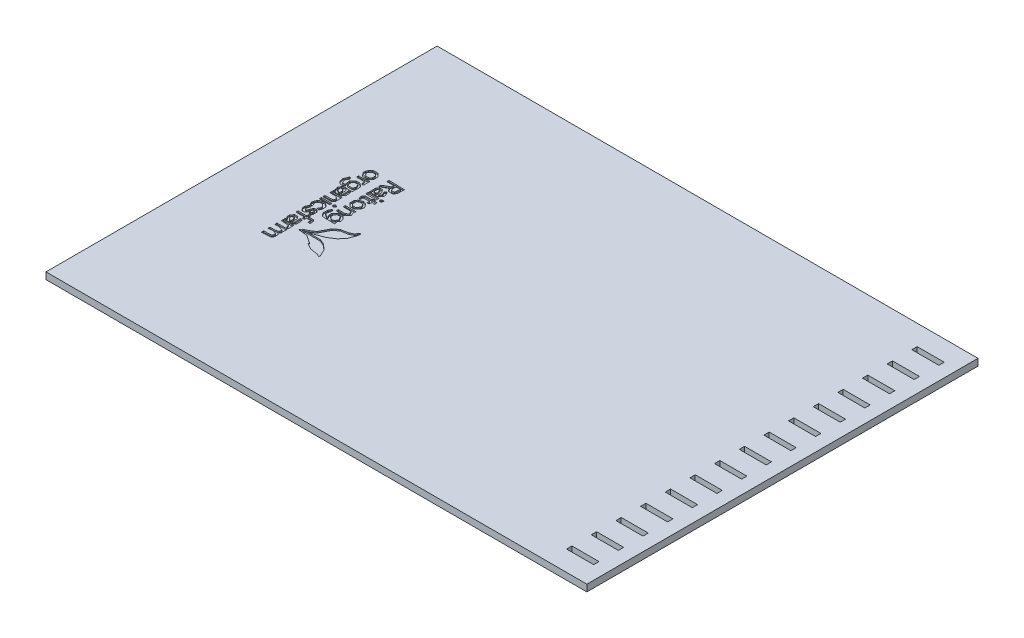
SolidWorks part; units mm, degrees
material "ABS"
ref_plane "Front Plane" through (0, 0, 0) normal (0, 0, 1) x (1, 0, 0)
ref_plane "Top Plane" through (0, 0, 0) normal (0, 1, 0) x (1, 0, 0)
ref_plane "Right Plane" through (0, 0, 0) normal (1, 0, 0) x (0, 0, -1)
sketch "Sketch1" plane through (0, 0, 0) normal (0, 1, 0) x (1, 0, 0)
  line L1 (-66.3921, 26.4776) -> (136.8079, 26.4776)
  line L2 (-66.3921, 26.4776) -> (-66.3921, -120.4614)
  line L3 (-66.3921, -120.4614) -> (136.8079, -120.4614)
  line L4 (136.8079, 26.4776) -> (136.8079, -120.4614)
  dimension "D1" = 203.2
  dimension "D2" = 146.939
extrude "Boss-Extrude1" add sketch "Sketch1" along normal blind 2.54
sketch "Sketch2" plane through (0, 2.54, 0) normal (0, 1, 0) x (0, 0, -1)
  line L14 (-120.4614, 66.3921) -> (-120.4614, -136.8079) construction
  line L15 (-110.8414, -131.7279) -> (-112.8414, -131.7279)
  line L16 (-110.8414, -131.7279) -> (-110.8414, -121.5679)
  line L17 (-110.8414, -121.5679) -> (-112.8414, -121.5679)
  line L18 (-112.8414, -131.7279) -> (-112.8414, -121.5679)
  line L19 (-120.4614, -136.8079) -> (26.4776, -136.8079) construction
  dimension "D1" = 2
  dimension "D2" = 7.62
  dimension "D3" = 5.08
  dimension "D4" = 10.16
extrude "Cut-Extrude1" cut sketch "Sketch2" against normal blind 2.794
pattern_linear "LPattern1" count 15 spacing 9.2642 along (0, 0, -1) of "Cut-Extrude1"
sketch "Sketch6" plane through (0, 2.54, 0) normal (0, 1, 0) x (1, 0, 0)
  line L8 (-40.8388, -35.001) -> (-40.6941, -35.6624)
  line L9 (-40.6941, -35.6624) -> (-40.2044, -36.1615)
  line L10 (-40.2044, -36.1615) -> (-39.7146, -36.6606)
  line L11 (-39.7146, -36.6606) -> (-38.5681, -36.6606)
  line L12 (-38.5681, -36.6606) -> (-37.4215, -36.6606)
  line L13 (-37.4215, -36.6606) -> (-37.9989, -36.8742)
  line L14 (-37.9989, -36.8742) -> (-38.5762, -37.0878)
  line L15 (-38.5762, -37.0878) -> (-38.8728, -37.6419)
  line L16 (-38.8728, -37.6419) -> (-39.1693, -38.1959)
  line L17 (-39.1693, -38.1959) -> (-38.9717, -38.7813)
  line L18 (-38.9717, -38.7813) -> (-38.774, -39.3666)
  line L19 (-38.774, -39.3666) -> (-38.8413, -39.8296)
  line L20 (-38.8413, -39.8296) -> (-38.9087, -40.2926)
  line L21 (-38.9087, -40.2926) -> (-37.4957, -40.2926)
  line L22 (-37.4957, -40.2926) -> (-36.0827, -40.2926)
  line L23 (-36.0827, -40.2926) -> (-35.4947, -39.8807)
  line L24 (-35.4947, -39.8807) -> (-34.9067, -39.4689)
  line L25 (-34.9067, -39.4689) -> (-34.9067, -38.7118)
  line L26 (-34.9067, -38.7118) -> (-34.9067, -37.9547)
  line L27 (-34.9067, -37.9547) -> (-35.0673, -37.5362)
  line L28 (-35.0673, -37.5362) -> (-35.2279, -37.1176)
  line L29 (-35.2279, -37.1176) -> (-35.5804, -37.1176)
  line L30 (-35.5804, -37.1176) -> (-35.9329, -37.1176)
  line L31 (-35.9329, -37.1176) -> (-35.8828, -38.2136)
  line L32 (-35.8828, -38.2136) -> (-35.8327, -39.3097)
  line L33 (-35.8327, -39.3097) -> (-36.1634, -39.4263)
  line L34 (-36.1634, -39.4263) -> (-36.4942, -39.543)
  line L35 (-36.4942, -39.543) -> (-36.4942, -38.6138)
  line L36 (-36.4942, -38.6138) -> (-36.4942, -37.6846)
  line L37 (-36.4942, -37.6846) -> (-36.9099, -37.2688)
  line L38 (-36.9099, -37.2688) -> (-37.3257, -36.853)
  line L39 (-37.3257, -36.853) -> (-36.1446, -36.853)
  line L40 (-36.1446, -36.853) -> (-34.9635, -36.853)
  line L41 (-34.9635, -36.853) -> (-34.9414, -35.2798)
  line L42 (-34.9414, -35.2798) -> (-34.9193, -33.7065)
  line L43 (-34.9193, -33.7065) -> (-35.6101, -33.1631)
  line L44 (-35.6101, -33.1631) -> (-36.301, -32.6197)
  line L45 (-36.301, -32.6197) -> (-37.0129, -32.6197)
  line L46 (-37.0129, -32.6197) -> (-37.7249, -32.6197)
  line L47 (-37.7249, -32.6197) -> (-38.331, -33.2649)
  line L48 (-38.331, -33.2649) -> (-38.9371, -33.9101)
  line L49 (-38.9371, -33.9101) -> (-38.8271, -34.8524)
  line L50 (-38.8271, -34.8524) -> (-38.7171, -35.7947)
  line L51 (-38.7171, -35.7947) -> (-39.1988, -35.7947)
  line L52 (-39.1988, -35.7947) -> (-39.6805, -35.7947)
  line L53 (-39.6805, -35.7947) -> (-39.977, -35.1441)
  line L54 (-39.977, -35.1441) -> (-40.2734, -34.4935)
  line L55 (-40.2734, -34.4935) -> (-39.8801, -33.8873)
  line L56 (-39.8801, -33.8873) -> (-39.4868, -33.2812)
  line L57 (-39.4868, -33.2812) -> (-39.6, -32.9504)
  line L58 (-39.6, -32.9504) -> (-39.7133, -32.6197)
  line L59 (-39.7133, -32.6197) -> (-39.9686, -32.6197)
  line L60 (-39.9686, -32.6197) -> (-40.2239, -32.6197)
  line L61 (-40.2239, -32.6197) -> (-40.6036, -33.4796)
  line L62 (-40.6036, -33.4796) -> (-40.9834, -34.3395)
  line L63 (-40.9834, -34.3395) -> (-40.8388, -35.001)
  line L64 (-38.3463, -38.4468) -> (-38.3463, -37.9426)
  line L65 (-38.3463, -37.9426) -> (-38.0415, -37.7543)
  line L66 (-38.0415, -37.7543) -> (-37.7368, -37.5659)
  line L67 (-37.7368, -37.5659) -> (-37.3801, -38.0538)
  line L68 (-37.3801, -38.0538) -> (-37.0233, -38.5417)
  line L69 (-37.0233, -38.5417) -> (-37.0233, -39.0203)
  line L70 (-37.0233, -39.0203) -> (-37.0233, -39.4989)
  line L71 (-37.0233, -39.4989) -> (-37.173, -39.4989)
  line L72 (-37.173, -39.4989) -> (-37.3227, -39.4989)
  line L73 (-37.3227, -39.4989) -> (-37.8345, -39.225)
  line L74 (-37.8345, -39.225) -> (-38.3463, -38.9511)
  line L75 (-38.3463, -38.9511) -> (-38.3463, -38.4468)
  line L76 (-38.0274, -34.8674) -> (-38.1055, -34.0723)
  line L77 (-38.1055, -34.0723) -> (-37.7761, -33.7429)
  line L78 (-37.7761, -33.7429) -> (-37.4467, -33.4135)
  line L79 (-37.4467, -33.4135) -> (-36.8324, -33.4135)
  line L80 (-36.8324, -33.4135) -> (-36.2183, -33.4135)
  line L81 (-36.2183, -33.4135) -> (-35.9075, -34.0955)
  line L82 (-35.9075, -34.0955) -> (-35.5968, -34.7775)
  line L83 (-35.5968, -34.7775) -> (-35.8759, -35.22)
  line L84 (-35.8759, -35.22) -> (-36.155, -35.6624)
  line L85 (-36.155, -35.6624) -> (-37.0522, -35.6624)
  line L86 (-37.0522, -35.6624) -> (-37.9494, -35.6624)
  line L87 (-37.9494, -35.6624) -> (-38.0274, -34.8674)
  line L88 (-39.1191, -28.1522) -> (-39.14, -28.5796)
  line L89 (-39.14, -28.5796) -> (-38.5916, -29.2767)
  line L90 (-38.5916, -29.2767) -> (-38.0433, -29.9739)
  line L91 (-38.0433, -29.9739) -> (-37.0041, -29.9739)
  line L92 (-37.0041, -29.9739) -> (-35.965, -29.9739)
  line L93 (-35.965, -29.9739) -> (-35.4358, -29.4447)
  line L94 (-35.4358, -29.4447) -> (-34.9067, -28.9155)
  line L95 (-34.9067, -28.9155) -> (-34.9067, -28.0727)
  line L96 (-34.9067, -28.0727) -> (-34.9067, -27.2298)
  line L97 (-34.9067, -27.2298) -> (-35.482, -26.6175)
  line L98 (-35.482, -26.6175) -> (-36.0572, -26.0051)
  line L99 (-36.0572, -26.0051) -> (-37.0285, -26.0051)
  line L100 (-37.0285, -26.0051) -> (-37.9997, -26.0051)
  line L101 (-37.9997, -26.0051) -> (-38.403, -26.4682)
  line L102 (-38.403, -26.4682) -> (-38.8064, -26.9312)
  line L103 (-38.8064, -26.9312) -> (-38.9523, -27.328)
  line L104 (-38.9523, -27.328) -> (-39.0982, -27.7249)
  line L105 (-39.0982, -27.7249) -> (-39.1191, -28.1522)
  line L106 (-38.3463, -27.8935) -> (-38.3463, -27.6304)
  line L107 (-38.3463, -27.6304) -> (-37.9305, -27.2147)
  line L108 (-37.9305, -27.2147) -> (-37.5147, -26.7989)
  line L109 (-37.5147, -26.7989) -> (-36.9251, -26.7989)
  line L110 (-36.9251, -26.7989) -> (-36.3354, -26.7989)
  line L111 (-36.3354, -26.7989) -> (-36.0179, -27.1164)
  line L112 (-36.0179, -27.1164) -> (-35.7004, -27.4339)
  line L113 (-35.7004, -27.4339) -> (-35.7004, -27.9895)
  line L114 (-35.7004, -27.9895) -> (-35.7004, -28.5451)
  line L115 (-35.7004, -28.5451) -> (-36.0179, -28.8626)
  line L116 (-36.0179, -28.8626) -> (-36.3354, -29.1801)
  line L117 (-36.3354, -29.1801) -> (-37.0669, -29.1801)
  line L118 (-37.0669, -29.1801) -> (-37.7985, -29.1801)
  line L119 (-37.7985, -29.1801) -> (-38.0724, -28.6684)
  line L120 (-38.0724, -28.6684) -> (-38.3463, -28.1566)
  line L121 (-38.3463, -28.1566) -> (-38.3463, -27.8935)
  line L122 (-39.1232, -47.6522) -> (-39.14, -48.0003)
  line L123 (-39.14, -48.0003) -> (-38.8661, -48.5121)
  line L124 (-38.8661, -48.5121) -> (-38.5922, -49.0239)
  line L125 (-38.5922, -49.0239) -> (-38.1764, -49.0239)
  line L126 (-38.1764, -49.0239) -> (-37.7605, -49.0239)
  line L127 (-37.7605, -49.0239) -> (-37.9511, -48.5609)
  line L128 (-37.9511, -48.5609) -> (-38.1417, -48.0978)
  line L129 (-38.1417, -48.0978) -> (-38.2645, -47.6743)
  line L130 (-38.2645, -47.6743) -> (-38.3873, -47.2507)
  line L131 (-38.3873, -47.2507) -> (-37.951, -46.8144)
  line L132 (-37.951, -46.8144) -> (-37.5147, -46.378)
  line L133 (-37.5147, -46.378) -> (-37.0233, -46.378)
  line L134 (-37.0233, -46.378) -> (-36.532, -46.378)
  line L135 (-36.532, -46.378) -> (-36.1162, -46.7938)
  line L136 (-36.1162, -46.7938) -> (-35.7004, -47.2096)
  line L137 (-35.7004, -47.2096) -> (-35.7004, -47.6669)
  line L138 (-35.7004, -47.6669) -> (-35.7004, -48.1243)
  line L139 (-35.7004, -48.1243) -> (-36.0093, -48.4331)
  line L140 (-36.0093, -48.4331) -> (-36.3181, -48.7419)
  line L141 (-36.3181, -48.7419) -> (-35.8503, -48.9215)
  line L142 (-35.8503, -48.9215) -> (-35.3824, -49.101)
  line L143 (-35.3824, -49.101) -> (-35.1486, -48.7317)
  line L144 (-35.1486, -48.7317) -> (-34.9148, -48.3624)
  line L145 (-34.9148, -48.3624) -> (-34.9107, -47.5217)
  line L146 (-34.9107, -47.5217) -> (-34.9067, -46.681)
  line L147 (-34.9067, -46.681) -> (-35.6038, -46.1327)
  line L148 (-35.6038, -46.1327) -> (-36.301, -45.5843)
  line L149 (-36.301, -45.5843) -> (-36.9441, -45.5843)
  line L150 (-36.9441, -45.5843) -> (-37.5873, -45.5843)
  line L151 (-37.5873, -45.5843) -> (-38.114, -45.8662)
  line L152 (-38.114, -45.8662) -> (-38.6407, -46.148)
  line L153 (-38.6407, -46.148) -> (-38.8736, -46.7261)
  line L154 (-38.8736, -46.7261) -> (-39.1065, -47.3041)
  line L155 (-39.1065, -47.3041) -> (-39.1232, -47.6522)
  line L156 (-39.1221, -50.8832) -> (-39.1401, -51.2874)
  line L157 (-39.1401, -51.2874) -> (-38.7282, -51.8754)
  line L158 (-38.7282, -51.8754) -> (-38.3162, -52.4635)
  line L159 (-38.3162, -52.4635) -> (-37.8171, -52.4635)
  line L160 (-37.8171, -52.4635) -> (-37.3179, -52.4635)
  line L161 (-37.3179, -52.4635) -> (-36.9061, -51.8754)
  line L162 (-36.9061, -51.8754) -> (-36.4942, -51.2874)
  line L163 (-36.4942, -51.2874) -> (-36.4942, -50.8171)
  line L164 (-36.4942, -50.8171) -> (-36.4942, -50.3468)
  line L165 (-36.4942, -50.3468) -> (-36.0973, -50.3468)
  line L166 (-36.0973, -50.3468) -> (-35.7004, -50.3468)
  line L167 (-35.7004, -50.3468) -> (-35.7004, -50.728)
  line L168 (-35.7004, -50.728) -> (-35.7004, -51.1093)
  line L169 (-35.7004, -51.1093) -> (-35.965, -51.2728)
  line L170 (-35.965, -51.2728) -> (-36.2296, -51.4364)
  line L171 (-36.2296, -51.4364) -> (-36.2296, -51.6936)
  line L172 (-36.2296, -51.6936) -> (-36.2296, -51.9509)
  line L173 (-36.2296, -51.9509) -> (-35.806, -52.1134)
  line L174 (-35.806, -52.1134) -> (-35.3824, -52.276)
  line L175 (-35.3824, -52.276) -> (-35.1486, -51.9067)
  line L176 (-35.1486, -51.9067) -> (-34.9148, -51.5374)
  line L177 (-34.9148, -51.5374) -> (-34.9107, -50.8508)
  line L178 (-34.9107, -50.8508) -> (-34.9067, -50.1642)
  line L179 (-34.9067, -50.1642) -> (-35.426, -49.6942)
  line L180 (-35.426, -49.6942) -> (-35.9453, -49.2243)
  line L181 (-35.9453, -49.2243) -> (-36.364, -49.3849)
  line L182 (-36.364, -49.3849) -> (-36.7827, -49.5456)
  line L183 (-36.7827, -49.5456) -> (-37.1788, -50.4937)
  line L184 (-37.1788, -50.4937) -> (-37.5749, -51.4418)
  line L185 (-37.5749, -51.4418) -> (-37.8944, -51.3288)
  line L186 (-37.8944, -51.3288) -> (-38.214, -51.2159)
  line L187 (-38.214, -51.2159) -> (-38.1648, -50.8475)
  line L188 (-38.1648, -50.8475) -> (-38.1156, -50.4791)
  line L189 (-38.1156, -50.4791) -> (-37.9355, -49.8838)
  line L190 (-37.9355, -49.8838) -> (-37.7554, -49.2885)
  line L191 (-37.7554, -49.2885) -> (-38.1427, -49.2885)
  line L192 (-38.1427, -49.2885) -> (-38.53, -49.2885)
  line L193 (-38.53, -49.2885) -> (-38.8171, -49.8838)
  line L194 (-38.8171, -49.8838) -> (-39.1042, -50.4791)
  line L195 (-39.1042, -50.4791) -> (-39.1221, -50.8832)
  line L196 (-39.1401, -56.7401) -> (-39.1401, -57.1947)
  line L197 (-39.1401, -57.1947) -> (-38.9003, -57.3429)
  line L198 (-38.9003, -57.3429) -> (-38.6606, -57.4911)
  line L199 (-38.6606, -57.4911) -> (-38.7989, -58.02)
  line L200 (-38.7989, -58.02) -> (-38.9372, -58.5489)
  line L201 (-38.9372, -58.5489) -> (-37.3378, -58.5489)
  line L202 (-37.3378, -58.5489) -> (-35.7383, -58.5489)
  line L203 (-35.7383, -58.5489) -> (-35.3225, -58.1331)
  line L204 (-35.3225, -58.1331) -> (-34.9067, -57.7173)
  line L205 (-34.9067, -57.7173) -> (-34.9067, -56.9641)
  line L206 (-34.9067, -56.9641) -> (-34.9067, -56.2109)
  line L207 (-34.9067, -56.2109) -> (-35.0674, -55.7924)
  line L208 (-35.0674, -55.7924) -> (-35.228, -55.3739)
  line L209 (-35.228, -55.3739) -> (-35.6013, -55.3739)
  line L210 (-35.6013, -55.3739) -> (-35.9747, -55.3739)
  line L211 (-35.9747, -55.3739) -> (-35.9037, -56.4698)
  line L212 (-35.9037, -56.4698) -> (-35.8328, -57.5658)
  line L213 (-35.8328, -57.5658) -> (-36.1635, -57.6825)
  line L214 (-36.1635, -57.6825) -> (-36.4942, -57.7992)
  line L215 (-36.4942, -57.7992) -> (-36.4942, -56.87)
  line L216 (-36.4942, -56.87) -> (-36.4942, -55.9408)
  line L217 (-36.4942, -55.9408) -> (-36.91, -55.5251)
  line L218 (-36.91, -55.5251) -> (-37.3258, -55.1093)
  line L219 (-37.3258, -55.1093) -> (-37.8211, -55.1093)
  line L220 (-37.8211, -55.1093) -> (-38.3163, -55.1093)
  line L221 (-38.3163, -55.1093) -> (-38.7282, -55.6973)
  line L222 (-38.7282, -55.6973) -> (-39.1401, -56.2854)
  line L223 (-39.1401, -56.2854) -> (-39.1401, -56.7401)
  line L224 (-38.3463, -56.8086) -> (-38.3463, -56.497)
  line L225 (-38.3463, -56.497) -> (-37.9679, -56.183)
  line L226 (-37.9679, -56.183) -> (-37.5895, -55.8689)
  line L227 (-37.5895, -55.8689) -> (-37.3065, -56.3977)
  line L228 (-37.3065, -56.3977) -> (-37.0234, -56.9266)
  line L229 (-37.0234, -56.9266) -> (-37.0234, -57.3409)
  line L230 (-37.0234, -57.3409) -> (-37.0234, -57.7551)
  line L231 (-37.0234, -57.7551) -> (-37.3674, -57.7551)
  line L232 (-37.3674, -57.7551) -> (-37.7113, -57.7551)
  line L233 (-37.7113, -57.7551) -> (-38.0288, -57.4376)
  line L234 (-38.0288, -57.4376) -> (-38.3463, -57.1201)
  line L235 (-38.3463, -57.1201) -> (-38.3463, -56.8086)
  line L236 (-38.8754, -30.8999) -> (-38.8754, -31.2968)
  line L237 (-38.8754, -31.2968) -> (-37.4253, -31.2968)
  line L238 (-37.4253, -31.2968) -> (-35.9751, -31.2968)
  line L239 (-35.9751, -31.2968) -> (-35.8091, -31.9583)
  line L240 (-35.8091, -31.9583) -> (-35.643, -32.6197)
  line L241 (-35.643, -32.6197) -> (-35.2845, -32.6197)
  line L242 (-35.2845, -32.6197) -> (-34.926, -32.6197)
  line L243 (-34.926, -32.6197) -> (-34.9505, -31.3963)
  line L244 (-34.9505, -31.3963) -> (-34.9751, -30.1728)
  line L245 (-34.9751, -30.1728) -> (-36.3299, -30.3357)
  line L246 (-36.3299, -30.3357) -> (-37.6848, -30.4984)
  line L247 (-37.6848, -30.4984) -> (-38.2801, -30.5008)
  line L248 (-38.2801, -30.5008) -> (-38.8754, -30.503)
  line L249 (-38.8754, -30.503) -> (-38.8754, -30.8999)
  line L250 (-38.8754, -40.9541) -> (-38.8754, -41.351)
  line L251 (-38.8754, -41.351) -> (-37.7354, -41.351)
  line L252 (-37.7354, -41.351) -> (-36.5953, -41.351)
  line L253 (-36.5953, -41.351) -> (-36.1191, -41.6992)
  line L254 (-36.1191, -41.6992) -> (-35.6429, -42.0474)
  line L255 (-35.6429, -42.0474) -> (-35.7404, -42.5591)
  line L256 (-35.7404, -42.5591) -> (-35.8379, -43.0708)
  line L257 (-35.8379, -43.0708) -> (-37.3566, -43.1501)
  line L258 (-37.3566, -43.1501) -> (-38.8754, -43.2295)
  line L259 (-38.8754, -43.2295) -> (-38.8754, -43.6131)
  line L260 (-38.8754, -43.6131) -> (-38.8754, -43.9968)
  line L261 (-38.8754, -43.9968) -> (-37.3068, -43.9968)
  line L262 (-37.3068, -43.9968) -> (-35.7382, -43.9968)
  line L263 (-35.7382, -43.9968) -> (-35.3275, -43.5861)
  line L264 (-35.3275, -43.5861) -> (-34.9168, -43.1754)
  line L265 (-34.9168, -43.1754) -> (-34.9463, -41.8663)
  line L266 (-34.9463, -41.8663) -> (-34.9758, -40.5572)
  line L267 (-34.9758, -40.5572) -> (-36.9256, -40.5572)
  line L268 (-36.9256, -40.5572) -> (-38.8754, -40.5572)
  line L269 (-38.8754, -40.5572) -> (-38.8754, -40.9541)
  line L270 (-38.8754, -44.9228) -> (-38.8754, -45.3197)
  line L271 (-38.8754, -45.3197) -> (-36.891, -45.3197)
  line L272 (-36.891, -45.3197) -> (-34.9067, -45.3197)
  line L273 (-34.9067, -45.3197) -> (-34.9067, -44.9228)
  line L274 (-34.9067, -44.9228) -> (-34.9067, -44.526)
  line L275 (-34.9067, -44.526) -> (-36.891, -44.526)
  line L276 (-36.891, -44.526) -> (-38.8754, -44.526)
  line L277 (-38.8754, -44.526) -> (-38.8754, -44.9228)
  line L278 (-38.8754, -53.6541) -> (-38.8754, -54.051)
  line L279 (-38.8754, -54.051) -> (-37.2879, -54.051)
  line L280 (-37.2879, -54.051) -> (-35.7004, -54.051)
  line L281 (-35.7004, -54.051) -> (-35.7004, -54.4478)
  line L282 (-35.7004, -54.4478) -> (-35.7004, -54.8447)
  line L283 (-35.7004, -54.8447) -> (-35.3035, -54.8447)
  line L284 (-35.3035, -54.8447) -> (-34.9067, -54.8447)
  line L285 (-34.9067, -54.8447) -> (-34.9067, -54.4478)
  line L286 (-34.9067, -54.4478) -> (-34.9067, -54.051)
  line L287 (-34.9067, -54.051) -> (-34.1129, -54.051)
  line L288 (-34.1129, -54.051) -> (-33.3192, -54.051)
  line L289 (-33.3192, -54.051) -> (-33.3192, -54.5801)
  line L290 (-33.3192, -54.5801) -> (-33.3192, -55.1093)
  line L291 (-33.3192, -55.1093) -> (-32.9223, -55.1093)
  line L292 (-32.9223, -55.1093) -> (-32.5254, -55.1093)
  line L293 (-32.5254, -55.1093) -> (-32.5254, -54.5008)
  line L294 (-32.5254, -54.5008) -> (-32.5254, -53.8922)
  line L295 (-32.5254, -53.8922) -> (-32.8429, -53.5747)
  line L296 (-32.8429, -53.5747) -> (-33.1604, -53.2572)
  line L297 (-33.1604, -53.2572) -> (-34.0335, -53.2572)
  line L298 (-34.0335, -53.2572) -> (-34.9067, -53.2572)
  line L299 (-34.9067, -53.2572) -> (-34.9067, -52.8603)
  line L300 (-34.9067, -52.8603) -> (-34.9067, -52.4635)
  line L301 (-34.9067, -52.4635) -> (-35.3035, -52.4635)
  line L302 (-35.3035, -52.4635) -> (-35.7004, -52.4635)
  line L303 (-35.7004, -52.4635) -> (-35.7004, -52.8603)
  line L304 (-35.7004, -52.8603) -> (-35.7004, -53.2572)
  line L305 (-35.7004, -53.2572) -> (-37.2879, -53.2572)
  line L306 (-37.2879, -53.2572) -> (-38.8754, -53.2572)
  line L307 (-38.8754, -53.2572) -> (-38.8754, -53.6541)
  line L308 (-38.8754, -59.1965) -> (-38.8754, -59.5796)
  line L309 (-38.8754, -59.5796) -> (-37.4863, -59.6595)
  line L310 (-37.4863, -59.6595) -> (-36.0973, -59.7395)
  line L311 (-36.0973, -59.7395) -> (-35.8361, -60.3348)
  line L312 (-35.8361, -60.3348) -> (-35.5749, -60.9301)
  line L313 (-35.5749, -60.9301) -> (-35.2574, -60.9301)
  line L314 (-35.2574, -60.9301) -> (-34.9398, -60.9301)
  line L315 (-34.9398, -60.9301) -> (-34.9544, -59.8718)
  line L316 (-34.9544, -59.8718) -> (-34.9691, -58.8135)
  line L317 (-34.9691, -58.8135) -> (-36.9222, -58.8135)
  line L318 (-36.9222, -58.8135) -> (-38.8754, -58.8135)
  line L319 (-38.8754, -58.8135) -> (-38.8754, -59.1965)
  line L320 (-38.8754, -61.5916) -> (-38.8754, -61.9885)
  line L321 (-38.8754, -61.9885) -> (-37.9666, -61.9885)
  line L322 (-37.9666, -61.9885) -> (-37.0578, -61.9885)
  line L323 (-37.0578, -61.9885) -> (-36.3791, -62.2465)
  line L324 (-36.3791, -62.2465) -> (-35.7004, -62.5045)
  line L325 (-35.7004, -62.5045) -> (-35.7004, -63.0094)
  line L326 (-35.7004, -63.0094) -> (-35.7004, -63.5143)
  line L327 (-35.7004, -63.5143) -> (-36.2957, -63.6738)
  line L328 (-36.2957, -63.6738) -> (-36.891, -63.8333)
  line L329 (-36.891, -63.8333) -> (-37.8832, -63.8369)
  line L330 (-37.8832, -63.8369) -> (-38.8754, -63.8406)
  line L331 (-38.8754, -63.8406) -> (-38.8754, -64.2208)
  line L332 (-38.8754, -64.2208) -> (-38.8754, -64.601)
  line L333 (-38.8754, -64.601) -> (-38.0155, -64.464)
  line L334 (-38.0155, -64.464) -> (-37.1556, -64.327)
  line L335 (-37.1556, -64.327) -> (-36.4097, -64.6134)
  line L336 (-36.4097, -64.6134) -> (-35.6637, -64.8997)
  line L337 (-35.6637, -64.8997) -> (-35.7482, -65.4946)
  line L338 (-35.7482, -65.4946) -> (-35.8327, -66.0895)
  line L339 (-35.8327, -66.0895) -> (-37.3541, -66.1689)
  line L340 (-37.3541, -66.1689) -> (-38.8754, -66.2482)
  line L341 (-38.8754, -66.2482) -> (-38.8754, -66.6627)
  line L342 (-38.8754, -66.6627) -> (-38.8754, -67.0772)
  line L343 (-38.8754, -67.0772) -> (-38.3374, -67.043)
  line L344 (-38.3374, -67.043) -> (-35.3996, -66.8559)
  line L345 (-35.3996, -66.8559) -> (-35.1572, -66.4727)
  line L346 (-35.1572, -66.4727) -> (-34.9148, -66.0895)
  line L347 (-34.9148, -66.0895) -> (-34.9107, -65.3775)
  line L348 (-34.9107, -65.3775) -> (-34.9067, -64.6655)
  line L349 (-34.9067, -64.6655) -> (-35.1841, -64.4941)
  line L350 (-35.1841, -64.4941) -> (-35.4615, -64.3226)
  line L351 (-35.4615, -64.3226) -> (-35.1928, -63.9988)
  line L352 (-35.1928, -63.9988) -> (-34.924, -63.6749)
  line L353 (-34.924, -63.6749) -> (-34.9489, -62.4348)
  line L354 (-34.9489, -62.4348) -> (-34.9738, -61.1947)
  line L355 (-34.9738, -61.1947) -> (-36.9246, -61.1947)
  line L356 (-36.9246, -61.1947) -> (-38.8754, -61.1947)
  line L357 (-38.8754, -61.1947) -> (-38.8754, -61.5916)
  line L358 (-34.1129, -44.9384) -> (-34.1129, -45.3197)
  line L359 (-34.1129, -45.3197) -> (-33.7317, -45.3197)
  line L360 (-33.7317, -45.3197) -> (-33.3504, -45.3197)
  line L361 (-33.3504, -45.3197) -> (-33.1686, -45.0255)
  line L362 (-33.1686, -45.0255) -> (-32.9868, -44.7314)
  line L363 (-32.9868, -44.7314) -> (-33.3388, -44.5138)
  line L364 (-33.3388, -44.5138) -> (-33.6908, -44.2963)
  line L365 (-33.6908, -44.2963) -> (-33.9018, -44.4267)
  line L366 (-33.9018, -44.4267) -> (-34.1129, -44.5572)
  line L367 (-34.1129, -44.5572) -> (-34.1129, -44.9384)
  line L368 (-33.5659, -48.3992) -> (-33.5838, -49.2298)
  line L369 (-33.5838, -49.2298) -> (-33.0782, -49.8545)
  line L370 (-33.0782, -49.8545) -> (-32.5725, -50.4791)
  line L371 (-32.5725, -50.4791) -> (-30.1296, -50.573)
  line L372 (-30.1296, -50.573) -> (-27.6867, -50.6669)
  line L373 (-27.6867, -50.6669) -> (-27.846, -50.0576)
  line L374 (-27.846, -50.0576) -> (-28.0054, -49.4483)
  line L375 (-28.0054, -49.4483) -> (-27.7223, -49.1072)
  line L376 (-27.7223, -49.1072) -> (-27.4392, -48.7662)
  line L377 (-27.4392, -48.7662) -> (-27.6043, -48.1086)
  line L378 (-27.6043, -48.1086) -> (-27.7693, -47.451)
  line L379 (-27.7693, -47.451) -> (-28.3452, -46.9145)
  line L380 (-28.3452, -46.9145) -> (-28.921, -46.378)
  line L381 (-28.921, -46.378) -> (-29.6769, -46.378)
  line L382 (-29.6769, -46.378) -> (-30.4328, -46.378)
  line L383 (-30.4328, -46.378) -> (-31.0822, -47.0275)
  line L384 (-31.0822, -47.0275) -> (-31.7317, -47.6769)
  line L385 (-31.7317, -47.6769) -> (-31.7317, -48.2355)
  line L386 (-31.7317, -48.2355) -> (-31.7317, -48.7941)
  line L387 (-31.7317, -48.7941) -> (-31.4578, -49.3059)
  line L388 (-31.4578, -49.3059) -> (-31.1839, -49.8176)
  line L389 (-31.1839, -49.8176) -> (-31.3989, -49.8176)
  line L390 (-31.3989, -49.8176) -> (-31.6139, -49.8176)
  line L391 (-31.6139, -49.8176) -> (-32.2272, -49.3881)
  line L392 (-32.2272, -49.3881) -> (-32.8405, -48.9585)
  line L393 (-32.8405, -48.9585) -> (-32.7016, -48.2636)
  line L394 (-32.7016, -48.2636) -> (-32.5628, -47.5687)
  line L395 (-32.5628, -47.5687) -> (-32.478, -47.068)
  line L396 (-32.478, -47.068) -> (-32.3931, -46.5673)
  line L397 (-32.3931, -46.5673) -> (-32.6801, -46.4652)
  line L398 (-32.6801, -46.4652) -> (-32.9671, -46.3631)
  line L399 (-32.9671, -46.3631) -> (-33.2575, -46.9659)
  line L400 (-33.2575, -46.9659) -> (-33.5479, -47.5687)
  line L401 (-33.5479, -47.5687) -> (-33.5659, -48.3992)
  line L402 (-30.9299, -48.5198) -> (-30.9218, -48.0978)
  line L403 (-30.9218, -48.0978) -> (-30.6521, -47.6348)
  line L404 (-30.6521, -47.6348) -> (-30.3825, -47.1718)
  line L405 (-30.3825, -47.1718) -> (-29.7403, -47.1718)
  line L406 (-29.7403, -47.1718) -> (-29.098, -47.1718)
  line L407 (-29.098, -47.1718) -> (-28.6763, -47.8155)
  line L408 (-28.6763, -47.8155) -> (-28.2545, -48.4592)
  line L409 (-28.2545, -48.4592) -> (-28.5376, -48.9882)
  line L410 (-28.5376, -48.9882) -> (-28.8207, -49.5172)
  line L411 (-28.8207, -49.5172) -> (-29.3691, -49.6913)
  line L412 (-29.3691, -49.6913) -> (-29.9175, -49.8653)
  line L413 (-29.9175, -49.8653) -> (-30.4277, -49.4036)
  line L414 (-30.4277, -49.4036) -> (-30.9379, -48.9419)
  line L415 (-30.9379, -48.9419) -> (-30.9299, -48.5198)
  line L416 (-31.0663, -59.3896) -> (-29.2954, -59.5688)
  line L417 (-29.2954, -59.5688) -> (-27.8677, -60.5168)
  line L418 (-27.8677, -60.5168) -> (-26.44, -61.4647)
  line L419 (-26.44, -61.4647) -> (-26.44, -61.7154)
  line L420 (-26.44, -61.7154) -> (-26.44, -61.9662)
  line L421 (-26.44, -61.9662) -> (-25.3155, -62.6236)
  line L422 (-25.3155, -62.6236) -> (-24.191, -63.281)
  line L423 (-24.191, -63.281) -> (-22.5109, -63.5503)
  line L424 (-22.5109, -63.5503) -> (-20.8309, -63.8197)
  line L425 (-20.8309, -63.8197) -> (-20.4604, -64.1271)
  line L426 (-20.4604, -64.1271) -> (-20.09, -64.4345)
  line L427 (-20.09, -64.4345) -> (-20.0926, -64.0714)
  line L428 (-20.0926, -64.0714) -> (-20.0952, -63.7083)
  line L429 (-20.0952, -63.7083) -> (-20.7172, -62.3853)
  line L430 (-20.7172, -62.3853) -> (-21.3393, -61.0624)
  line L431 (-21.3393, -61.0624) -> (-22.3165, -60.183)
  line L432 (-22.3165, -60.183) -> (-23.2938, -59.3036)
  line L433 (-23.2938, -59.3036) -> (-24.2716, -58.8762)
  line L434 (-24.2716, -58.8762) -> (-25.2494, -58.4487)
  line L435 (-25.2494, -58.4487) -> (-27.9705, -58.4327)
  line L436 (-27.9705, -58.4327) -> (-30.6916, -58.4166)
  line L437 (-30.6916, -58.4166) -> (-29.703, -58.2111)
  line L438 (-29.703, -58.2111) -> (-28.7143, -58.0057)
  line L439 (-28.7143, -58.0057) -> (-26.8496, -57.3346)
  line L440 (-26.8496, -57.3346) -> (-24.9848, -56.6634)
  line L441 (-24.9848, -56.6634) -> (-23.7214, -55.8545)
  line L442 (-23.7214, -55.8545) -> (-22.458, -55.0456)
  line L443 (-22.458, -55.0456) -> (-21.5701, -54.0083)
  line L444 (-21.5701, -54.0083) -> (-20.6822, -52.971)
  line L445 (-20.6822, -52.971) -> (-20.1215, -51.4333)
  line L446 (-20.1215, -51.4333) -> (-19.5608, -49.8956)
  line L447 (-19.5608, -49.8956) -> (-19.5608, -49.4597)
  line L448 (-19.5608, -49.4597) -> (-19.5608, -49.0239)
  line L449 (-19.5608, -49.0239) -> (-19.8161, -49.0239)
  line L450 (-19.8161, -49.0239) -> (-20.0714, -49.0239)
  line L451 (-20.0714, -49.0239) -> (-20.3531, -49.5503)
  line L452 (-20.3531, -49.5503) -> (-20.6349, -50.0767)
  line L453 (-20.6349, -50.0767) -> (-21.4209, -50.4832)
  line L454 (-21.4209, -50.4832) -> (-22.207, -50.8897)
  line L455 (-22.207, -50.8897) -> (-23.5726, -51.1487)
  line L456 (-23.5726, -51.1487) -> (-24.9382, -51.4077)
  line L457 (-24.9382, -51.4077) -> (-25.8091, -52.072)
  line L458 (-25.8091, -52.072) -> (-26.68, -52.7362)
  line L459 (-26.68, -52.7362) -> (-27.6648, -54.6102)
  line L460 (-27.6648, -54.6102) -> (-28.6495, -56.4842)
  line L461 (-28.6495, -56.4842) -> (-29.6743, -57.1311)
  line L462 (-29.6743, -57.1311) -> (-30.6991, -57.778)
  line L463 (-30.6991, -57.778) -> (-31.4138, -58.0683)
  line L464 (-31.4138, -58.0683) -> (-32.1285, -58.3585)
  line L465 (-32.1285, -58.3585) -> (-31.4671, -58.5596)
  line L466 (-31.4671, -58.5596) -> (-30.8056, -58.7607)
  line L467 (-30.8056, -58.7607) -> (-31.6214, -58.7871)
  line L468 (-31.6214, -58.7871) -> (-32.4372, -58.8135)
  line L469 (-32.4372, -58.8135) -> (-32.6372, -59.0119)
  line L470 (-32.6372, -59.0119) -> (-32.8371, -59.2104)
  line L471 (-32.8371, -59.2104) -> (-31.0663, -59.3896)
  line L472 (-31.7317, -26.6579) -> (-31.7317, -27.0635)
  line L473 (-31.7317, -27.0635) -> (-30.3894, -27.0635)
  line L474 (-30.3894, -27.0635) -> (-29.047, -27.0635)
  line L475 (-29.047, -27.0635) -> (-29.1355, -27.5229)
  line L476 (-29.1355, -27.5229) -> (-29.224, -27.9824)
  line L477 (-29.224, -27.9824) -> (-30.3657, -28.6122)
  line L478 (-30.3657, -28.6122) -> (-31.5075, -29.242)
  line L479 (-31.5075, -29.242) -> (-31.6522, -29.6194)
  line L480 (-31.6522, -29.6194) -> (-31.7971, -29.9967)
  line L481 (-31.7971, -29.9967) -> (-31.6723, -30.1214)
  line L482 (-31.6723, -30.1214) -> (-31.5475, -30.2462)
  line L483 (-31.5475, -30.2462) -> (-30.2985, -29.5481)
  line L484 (-30.2985, -29.5481) -> (-29.0494, -28.8499)
  line L485 (-29.0494, -28.8499) -> (-28.6557, -29.4119)
  line L486 (-28.6557, -29.4119) -> (-28.2621, -29.9739)
  line L487 (-28.2621, -29.9739) -> (-27.3604, -29.9739)
  line L488 (-27.3604, -29.9739) -> (-26.4586, -29.9739)
  line L489 (-26.4586, -29.9739) -> (-26.1588, -29.4136)
  line L490 (-26.1588, -29.4136) -> (-25.8589, -28.8533)
  line L491 (-25.8589, -28.8533) -> (-25.8187, -27.6276)
  line L492 (-25.8187, -27.6276) -> (-25.7785, -26.402)
  line L493 (-25.7785, -26.402) -> (-28.7551, -26.3272)
  line L494 (-28.7551, -26.3272) -> (-31.7317, -26.2524)
  line L495 (-31.7317, -26.2524) -> (-31.7317, -26.6579)
  line L496 (-28.288, -27.7911) -> (-28.2921, -27.0635)
  line L497 (-28.2921, -27.0635) -> (-27.4824, -27.0635)
  line L498 (-27.4824, -27.0635) -> (-26.6727, -27.0635)
  line L499 (-26.6727, -27.0635) -> (-26.7548, -28.0534)
  line L500 (-26.7548, -28.0534) -> (-26.8369, -29.0434)
  line L501 (-26.8369, -29.0434) -> (-27.3343, -29.1378)
  line L502 (-27.3343, -29.1378) -> (-27.8318, -29.2322)
  line L503 (-27.8318, -29.2322) -> (-28.0579, -28.8754)
  line L504 (-28.0579, -28.8754) -> (-28.284, -28.5187)
  line L505 (-28.284, -28.5187) -> (-28.288, -27.7911)
  line L506 (-31.6913, -32.4022) -> (-31.6625, -33.678)
  line L507 (-31.6625, -33.678) -> (-30.1096, -33.678)
  line L508 (-30.1096, -33.678) -> (-28.5567, -33.678)
  line L509 (-28.5567, -33.678) -> (-28.0275, -33.1489)
  line L510 (-28.0275, -33.1489) -> (-27.4983, -32.6197)
  line L511 (-27.4983, -32.6197) -> (-27.4983, -32.2353)
  line L512 (-27.4983, -32.2353) -> (-27.4983, -31.8509)
  line L513 (-27.4983, -31.8509) -> (-27.8054, -31.177)
  line L514 (-27.8054, -31.177) -> (-28.1125, -30.503)
  line L515 (-28.1125, -30.503) -> (-28.319, -30.503)
  line L516 (-28.319, -30.503) -> (-28.5254, -30.503)
  line L517 (-28.5254, -30.503) -> (-28.6856, -30.7621)
  line L518 (-28.6856, -30.7621) -> (-28.8457, -31.0213)
  line L519 (-28.8457, -31.0213) -> (-28.5699, -31.5367)
  line L520 (-28.5699, -31.5367) -> (-28.294, -32.0522)
  line L521 (-28.294, -32.0522) -> (-28.4536, -32.4682)
  line L522 (-28.4536, -32.4682) -> (-28.6133, -32.8843)
  line L523 (-28.6133, -32.8843) -> (-28.8496, -32.8843)
  line L524 (-28.8496, -32.8843) -> (-29.0858, -32.8843)
  line L525 (-29.0858, -32.8843) -> (-29.0858, -32.2817)
  line L526 (-29.0858, -32.2817) -> (-29.0858, -31.6791)
  line L527 (-29.0858, -31.6791) -> (-29.4977, -31.0911)
  line L528 (-29.4977, -31.0911) -> (-29.9096, -30.503)
  line L529 (-29.9096, -30.503) -> (-30.5031, -30.503)
  line L530 (-30.5031, -30.503) -> (-31.0967, -30.503)
  line L531 (-31.0967, -30.503) -> (-31.4084, -30.8147)
  line L532 (-31.4084, -30.8147) -> (-31.72, -31.1264)
  line L533 (-31.72, -31.1264) -> (-31.6913, -32.4022)
  line L534 (-30.9379, -31.9666) -> (-30.9379, -31.2968)
  line L535 (-30.9379, -31.2968) -> (-30.5461, -31.2968)
  line L536 (-30.5461, -31.2968) -> (-30.1543, -31.2968)
  line L537 (-30.1543, -31.2968) -> (-29.9851, -31.9706)
  line L538 (-29.9851, -31.9706) -> (-29.816, -32.6444)
  line L539 (-29.816, -32.6444) -> (-29.9687, -32.797)
  line L540 (-29.9687, -32.797) -> (-30.1213, -32.9497)
  line L541 (-30.1213, -32.9497) -> (-30.5296, -32.793)
  line L542 (-30.5296, -32.793) -> (-30.9379, -32.6363)
  line L543 (-30.9379, -32.6363) -> (-30.9379, -31.9666)
  line L544 (-31.7317, -34.4718) -> (-31.7317, -35.001)
  line L545 (-31.7317, -35.001) -> (-30.0202, -35.001)
  line L546 (-30.0202, -35.001) -> (-28.3087, -35.001)
  line L547 (-28.3087, -35.001) -> (-28.461, -35.3978)
  line L548 (-28.461, -35.3978) -> (-28.6133, -35.7947)
  line L549 (-28.6133, -35.7947) -> (-29.8755, -35.7947)
  line L550 (-29.8755, -35.7947) -> (-31.1377, -35.7947)
  line L551 (-31.1377, -35.7947) -> (-31.455, -36.177)
  line L552 (-31.455, -36.177) -> (-31.7723, -36.5593)
  line L553 (-31.7723, -36.5593) -> (-31.6858, -37.1485)
  line L554 (-31.6858, -37.1485) -> (-31.5994, -37.7376)
  line L555 (-31.5994, -37.7376) -> (-31.2687, -37.8466)
  line L556 (-31.2687, -37.8466) -> (-30.9379, -37.9555)
  line L557 (-30.9379, -37.9555) -> (-30.9379, -37.4309)
  line L558 (-30.9379, -37.4309) -> (-30.9379, -36.9063)
  line L559 (-30.9379, -36.9063) -> (-29.7473, -36.8116)
  line L560 (-29.7473, -36.8116) -> (-28.5567, -36.717)
  line L561 (-28.5567, -36.717) -> (-28.5567, -37.1819)
  line L562 (-28.5567, -37.1819) -> (-28.5567, -37.6468)
  line L563 (-28.5567, -37.6468) -> (-28.1598, -37.6468)
  line L564 (-28.1598, -37.6468) -> (-27.7629, -37.6468)
  line L565 (-27.7629, -37.6468) -> (-27.7629, -37.1424)
  line L566 (-27.7629, -37.1424) -> (-27.7629, -36.638)
  line L567 (-27.7629, -36.638) -> (-27.2338, -36.7764)
  line L568 (-27.2338, -36.7764) -> (-26.7046, -36.9148)
  line L569 (-26.7046, -36.9148) -> (-26.7046, -36.3547)
  line L570 (-26.7046, -36.3547) -> (-26.7046, -35.7947)
  line L571 (-26.7046, -35.7947) -> (-27.2338, -35.7947)
  line L572 (-27.2338, -35.7947) -> (-27.7629, -35.7947)
  line L573 (-27.7629, -35.7947) -> (-27.7629, -34.8687)
  line L574 (-27.7629, -34.8687) -> (-27.7629, -33.9426)
  line L575 (-27.7629, -33.9426) -> (-29.7473, -33.9426)
  line L576 (-29.7473, -33.9426) -> (-31.7317, -33.9426)
  line L577 (-31.7317, -33.9426) -> (-31.7317, -34.4718)
  line L578 (-31.7317, -40.1277) -> (-31.7317, -40.92)
  line L579 (-31.7317, -40.92) -> (-31.1564, -41.5323)
  line L580 (-31.1564, -41.5323) -> (-30.5811, -42.1447)
  line L581 (-30.5811, -42.1447) -> (-29.7012, -42.1447)
  line L582 (-29.7012, -42.1447) -> (-28.8213, -42.1447)
  line L583 (-28.8213, -42.1447) -> (-28.2988, -41.6223)
  line L584 (-28.2988, -41.6223) -> (-27.7764, -41.0998)
  line L585 (-27.7764, -41.0998) -> (-27.6082, -40.4297)
  line L586 (-27.6082, -40.4297) -> (-27.44, -39.7596)
  line L587 (-27.44, -39.7596) -> (-27.8799, -39.0883)
  line L588 (-27.8799, -39.0883) -> (-28.3198, -38.4169)
  line L589 (-28.3198, -38.4169) -> (-28.9674, -38.1707)
  line L590 (-28.9674, -38.1707) -> (-29.615, -37.9245)
  line L591 (-29.615, -37.9245) -> (-30.3426, -38.1944)
  line L592 (-30.3426, -38.1944) -> (-31.0702, -38.4644)
  line L593 (-31.0702, -38.4644) -> (-31.4009, -38.8999)
  line L594 (-31.4009, -38.8999) -> (-31.7317, -39.3354)
  line L595 (-31.7317, -39.3354) -> (-31.7317, -40.1277)
  line L596 (-30.9379, -39.9666) -> (-30.9379, -39.2173)
  line L597 (-30.9379, -39.2173) -> (-30.3525, -39.0007)
  line L598 (-30.3525, -39.0007) -> (-29.767, -38.7841)
  line L599 (-29.767, -38.7841) -> (-29.2858, -38.91)
  line L600 (-29.2858, -38.91) -> (-28.8045, -39.0358)
  line L601 (-28.8045, -39.0358) -> (-28.5295, -39.5497)
  line L602 (-28.5295, -39.5497) -> (-28.2545, -40.0635)
  line L603 (-28.2545, -40.0635) -> (-28.6763, -40.7072)
  line L604 (-28.6763, -40.7072) -> (-29.098, -41.351)
  line L605 (-29.098, -41.351) -> (-29.7005, -41.351)
  line L606 (-29.7005, -41.351) -> (-30.3029, -41.351)
  line L607 (-30.3029, -41.351) -> (-30.6204, -41.0335)
  line L608 (-30.6204, -41.0335) -> (-30.9379, -40.716)
  line L609 (-30.9379, -40.716) -> (-30.9379, -39.9666)
  line L610 (-31.7317, -43.0708) -> (-31.7317, -43.4676)
  line L611 (-31.7317, -43.4676) -> (-30.2858, -43.4676)
  line L612 (-30.2858, -43.4676) -> (-28.8399, -43.4676)
  line L613 (-28.8399, -43.4676) -> (-28.5325, -44.042)
  line L614 (-28.5325, -44.042) -> (-28.2251, -44.6164)
  line L615 (-28.2251, -44.6164) -> (-28.706, -44.968)
  line L616 (-28.706, -44.968) -> (-29.187, -45.3197)
  line L617 (-29.187, -45.3197) -> (-30.4593, -45.3197)
  line L618 (-30.4593, -45.3197) -> (-31.7317, -45.3197)
  line L619 (-31.7317, -45.3197) -> (-31.7317, -45.7166)
  line L620 (-31.7317, -45.7166) -> (-31.7317, -46.1135)
  line L621 (-31.7317, -46.1135) -> (-30.2912, -46.1135)
  line L622 (-30.2912, -46.1135) -> (-28.8508, -46.1135)
  line L623 (-28.8508, -46.1135) -> (-28.1345, -45.4974)
  line L624 (-28.1345, -45.4974) -> (-27.4182, -44.8812)
  line L625 (-27.4182, -44.8812) -> (-27.6337, -44.1083)
  line L626 (-27.6337, -44.1083) -> (-27.8491, -43.3353)
  line L627 (-27.8491, -43.3353) -> (-27.7944, -43.0046)
  line L628 (-27.7944, -43.0046) -> (-27.7397, -42.6739)
  line L629 (-27.7397, -42.6739) -> (-29.7357, -42.6739)
  line L630 (-29.7357, -42.6739) -> (-31.7317, -42.6739)
  line L631 (-31.7317, -42.6739) -> (-31.7317, -43.0708)
  line L632 (-26.8865, -34.5875) -> (-26.7928, -34.8687)
  line L633 (-26.7928, -34.8687) -> (-26.4216, -34.8687)
  line L634 (-26.4216, -34.8687) -> (-26.0504, -34.8687)
  line L635 (-26.0504, -34.8687) -> (-25.9612, -34.4057)
  line L636 (-25.9612, -34.4057) -> (-25.872, -33.9426)
  line L637 (-25.872, -33.9426) -> (-26.2442, -33.9426)
  line L638 (-26.2442, -33.9426) -> (-26.6164, -33.9426)
  line L639 (-26.6164, -33.9426) -> (-26.7983, -34.1245)
  line L640 (-26.7983, -34.1245) -> (-26.9802, -34.3064)
  line L641 (-26.9802, -34.3064) -> (-26.8865, -34.5875)
extrude "Cut-Extrude2" cut sketch "Sketch6" against normal blind 0.508
